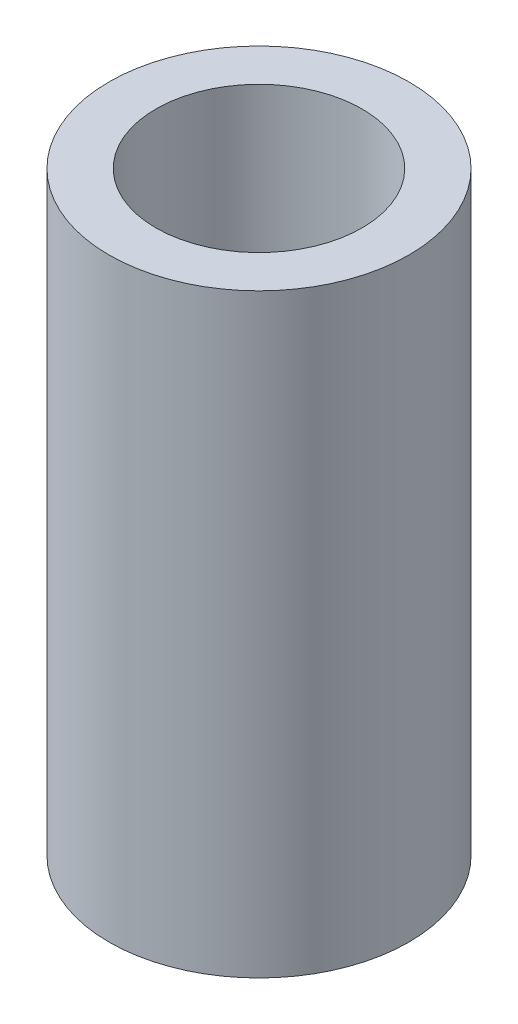
SolidWorks part; units mm, degrees
ref_plane "Front Plane" through (0, 0, 0) normal (0, 0, 1) x (1, 0, 0)
ref_plane "Top Plane" through (0, 0, 0) normal (0, 1, 0) x (1, 0, 0)
ref_plane "Right Plane" through (0, 0, 0) normal (1, 0, 0) x (0, 0, -1)
sketch "Sketch1" plane through (0, 0, 0) normal (0, 1, 0) x (1, 0, 0)
  circle A0 centre (0, 0) radius 3.2
  circle A1 centre (0, 0) radius 2.2
  dimension "D1" = 6.4
  dimension "D2" = 4.4
extrude "Boss-Extrude1" add sketch "Sketch1" along normal blind 12.7
